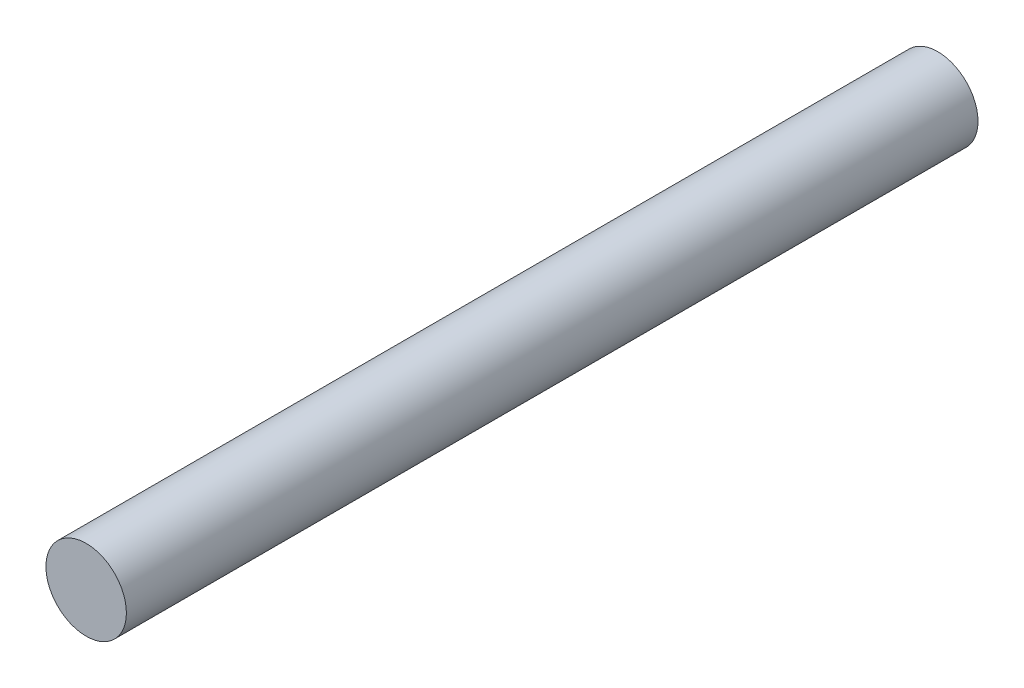
SolidWorks part; units mm, degrees
ref_plane "Front Plane" through (0, 0, 0) normal (0, 0, 1) x (1, 0, 0)
ref_plane "Top Plane" through (0, 0, 0) normal (0, 1, 0) x (1, 0, 0)
ref_plane "Right Plane" through (0, 0, 0) normal (1, 0, 0) x (0, 0, -1)
sketch "Sketch1" plane through (0, 0, 0) normal (0, 0, 1) x (1, 0, 0)
  circle A0 centre (0, 0) radius 3
  dimension "D1" = 6
extrude "Boss-Extrude1" add sketch "Sketch1" along normal blind 63.5
